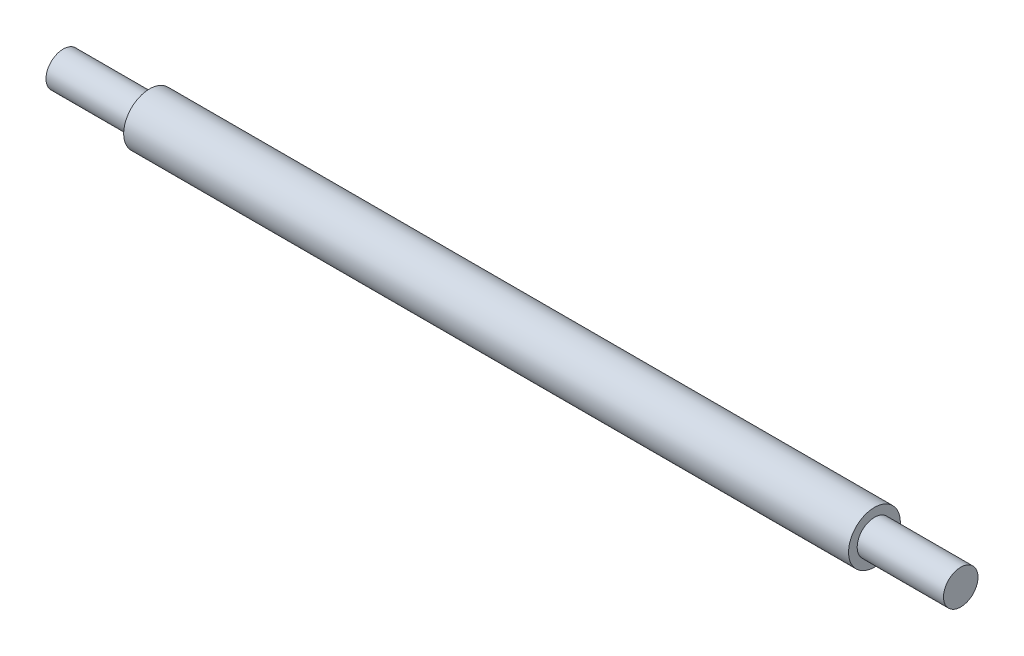
SolidWorks part; units mm, degrees
ref_plane "Front" through (0, 0, 0) normal (0, 0, 1) x (1, 0, 0)
ref_plane "Top" through (0, 0, 0) normal (0, 1, 0) x (1, 0, 0)
ref_plane "Right" through (0, 0, 0) normal (1, 0, 0) x (0, 0, -1)
sketch "Sketch1" plane through (0, 0, 0) normal (0, 0, 1) x (1, 0, 0)
  line L0 (-52, 0) -> (106.0373, 0) construction
  line L1 (-52, 0) -> (-52, 2)
  line L2 (-52, 2) -> (-42, 2)
  line L3 (-42, 2) -> (-42, 3)
  line L4 (-42, 3) -> (42, 3)
  line L5 (42, 3) -> (42, 2)
  line L6 (42, 2) -> (52, 2)
  line L7 (52, 2) -> (52, 0)
  line L8 (52, 0) -> (-52, 0)
  dimension "D1" = 6
  dimension "D2" = 4
  dimension "D3" = 104
  dimension "D4" = 10
  dimension "D5" = 10
revolve "Revolve1" add sketch "Sketch1" angle 360 about L0
